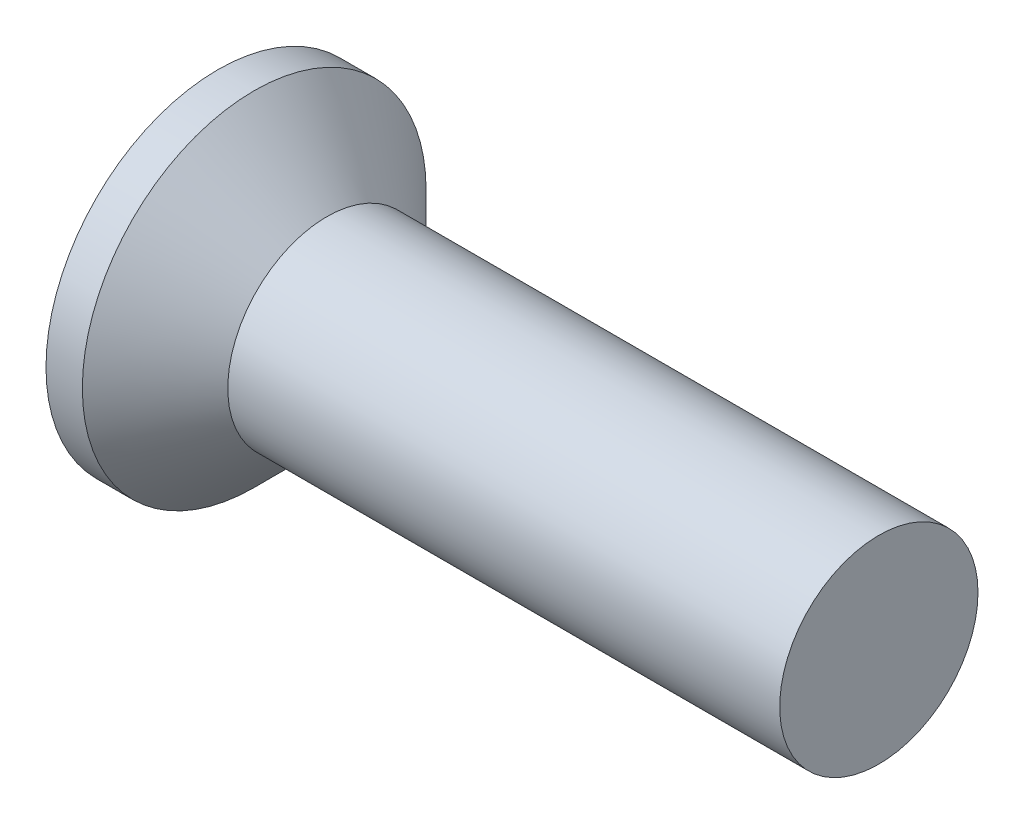
SolidWorks part; units mm, degrees
ref_plane "Front" through (0, 0, 0) normal (0, 0, 1) x (1, 0, 0)
ref_plane "Top" through (0, 0, 0) normal (0, 1, 0) x (1, 0, 0)
ref_plane "Right" through (0, 0, 0) normal (1, 0, 0) x (0, 0, -1)
sketch "Sketch1" plane through (0, 0, 0) normal (0, 0, 1) x (1, 0, 0)
  line L0 (10, 1.5) -> (2.65, 1.5)
  line L1 (2.65, 1.5) -> (1.65, 1.5)
  line L2 (1.65, 1.5) -> (0.55, 2.6)
  line L3 (0.55, 2.6) -> (0, 2.6)
  line L4 (10, 1.5) -> (10, 0)
  line L5 (4.5158, 0) -> (-89.8219, 0) construction
  line L6 (10, 0) -> (0, 0)
  line L7 (0, 2.6) -> (0, 0)
  dimension "d" = 3
  dimension "D1" = 45
  dimension "dk" = 5.2
  dimension "k" = 1.65
  dimension "l" = 10
  dimension "a" = 1
revolve "Base" add sketch "Sketch1" angle 360 about L5
cosmetic thread "ThreadCosmetic1" parameters "bb"=8.35, "THD_MINOR"=2.459
sketch "Sketch6" plane through (0, 0, 0) normal (1, 0, 0) x (0, 0, -1)
  line L0 (-1.9271, 0) -> (2.0512, 0) construction
  line L1 (0, 1.8651) -> (0, -2.0207) construction
  line L2 (0.32, 0.32) -> (0.32, 1.6)
  line L3 (0.32, 1.6) -> (-0.32, 1.6)
  line L4 (-0.32, 0.32) -> (-0.32, 1.6)
  line L5 (0.32, 0.32) -> (1.6, 0.32)
  line L6 (1.6, 0.32) -> (1.6, -0.32)
  line L7 (-1.6, 0.32) -> (-1.6, -0.32)
  line L8 (-0.32, 0.32) -> (-1.6, 0.32)
  line L9 (-0.32, -0.32) -> (-1.6, -0.32)
  line L10 (0.32, -0.32) -> (1.6, -0.32)
  line L11 (-0.32, -0.32) -> (-0.32, -1.6)
  line L12 (0.32, -1.6) -> (-0.32, -1.6)
  line L13 (0.32, -0.32) -> (0.32, -1.6)
  point P16 (-1.6, 0)
  point P17 (1.6, 0)
extrude "CrossRecess" cut sketch "Sketch6" along normal blind 0.825
draft "Draft9" type of draft neutral plane draft angle 30 faces to draft 4 face at (0.4125, 1.6, 0) face at (0.4125, 0, 1.6) face at (0.4125, -1.6, 0) face at (0.4125, 0, -1.6) neutral plane through (0, 2.6, 0) neutral plane normal (-1, 0, 0) parameters "D1"=30
fillet "Fillet5" radius 0.3 4 edges at (0.4125, -0.32, -0.32) (0.4125, 0.32, -0.32) (0.4125, 0.32, 0.32) (0.4125, -0.32, 0.32)
sketch "Sketch7" plane through (0, 0, 0) normal (1, 0, 0) x (0, 0, -1)
  line L0 (-2.0126, 0) -> (1.9757, 0) construction
  line L1 (0, 1.9314) -> (0, -2.0126) construction
  line L2 (0, 0) -> (1.5555, 1.5555) construction
  line L3 (0, 0.4782) -> (1.1314, 1.1314)
  line L4 (-1.5402, 1.5402) -> (0, 0) construction
  line L5 (0.4782, 0) -> (1.1314, 1.1314)
  line L6 (0, -0.4782) -> (1.1314, -1.1314)
  line L7 (0.4782, 0) -> (1.1314, -1.1314)
  line L8 (-0.4782, 0) -> (-1.1314, -1.1314)
  line L9 (0, -0.4782) -> (-1.1314, -1.1314)
  line L10 (-0.4782, 0) -> (-1.1314, 1.1314)
  line L11 (0, 0.4782) -> (-1.1314, 1.1314)
  dimension "D3" = 15
  dimension "m" = 3.2
extrude "Cut-Extrude3" [suppressed] cut sketch "Sketch7" along normal blind 10 draft 20
sketch "Sketch8" plane through (0, 0, 0) normal (0, 0, 1) x (1, 0, 0)
  line L0 (-15, 1.7705) -> (-16.25, 1.5)
  line L1 (-16.25, 1.5) -> (1.65, 1.5)
  line L3 (10, -1.5) -> (10, 1.5) construction
  line L6 (1.65, 1.5) -> (1.65, 6.5)
  line L7 (1.65, 6.5) -> (-15, 6.5)
  line L8 (-15, 6.5) -> (-15, 1.7705)
  line L9 (62.4753, 0.2705) -> (52.9594, 0.2705) construction
  dimension "D1" = 5
  dimension "x" = 1.25
  dimension "d" = 3
  dimension "THD_MINOR" = 2.459
  dimension "b" = 25
sketch "Sketch9" plane through (0, 0, 0) normal (0, 0, 1) x (1, 0, 0)
  line L0 (10, 1.2657) -> (10.1353, 1.5)
  line L1 (10.1353, 1.5) -> (10.1353, 1.7705)
  line L2 (10.1353, 1.7705) -> (9.8648, 1.7705)
  line L3 (9.8648, 1.7705) -> (9.8648, 1.5)
  line L4 (9.8648, 1.5) -> (10, 1.2657)
  line L5 (0, 0) -> (73.843, 0) construction
  line L6 (10, -1.5) -> (10, 1.5) construction
  dimension "D1" = 3
  dimension "D2" = 0.2705
revolve "Cut-Revolve10" [suppressed] cut sketch "Sketch9" angle 360 about L5
pattern_linear "LPattern10" [suppressed] count 26 spacing 0.3246 along (1, 0, 0)
equation "\"D1@Sketch6\" = \"m@Sketch6\" / 5"
equation "\"D1@CrossRecess\" = \"k@Sketch1\" / 2"
equation "\"D1@Sketch9\" = \"d@Sketch1\""
equation "\"D2@Sketch9\" =  ( \"d@Sketch1\" - \"THD_MINOR@ThreadCosmetic1\" )  / 2"
equation "\"D3@LPattern10\" = \"D2@Sketch9\" * 1.2"
equation "\"D1@LPattern10\" = \"bb@ThreadCosmetic1\" / \"D3@LPattern10\" "
